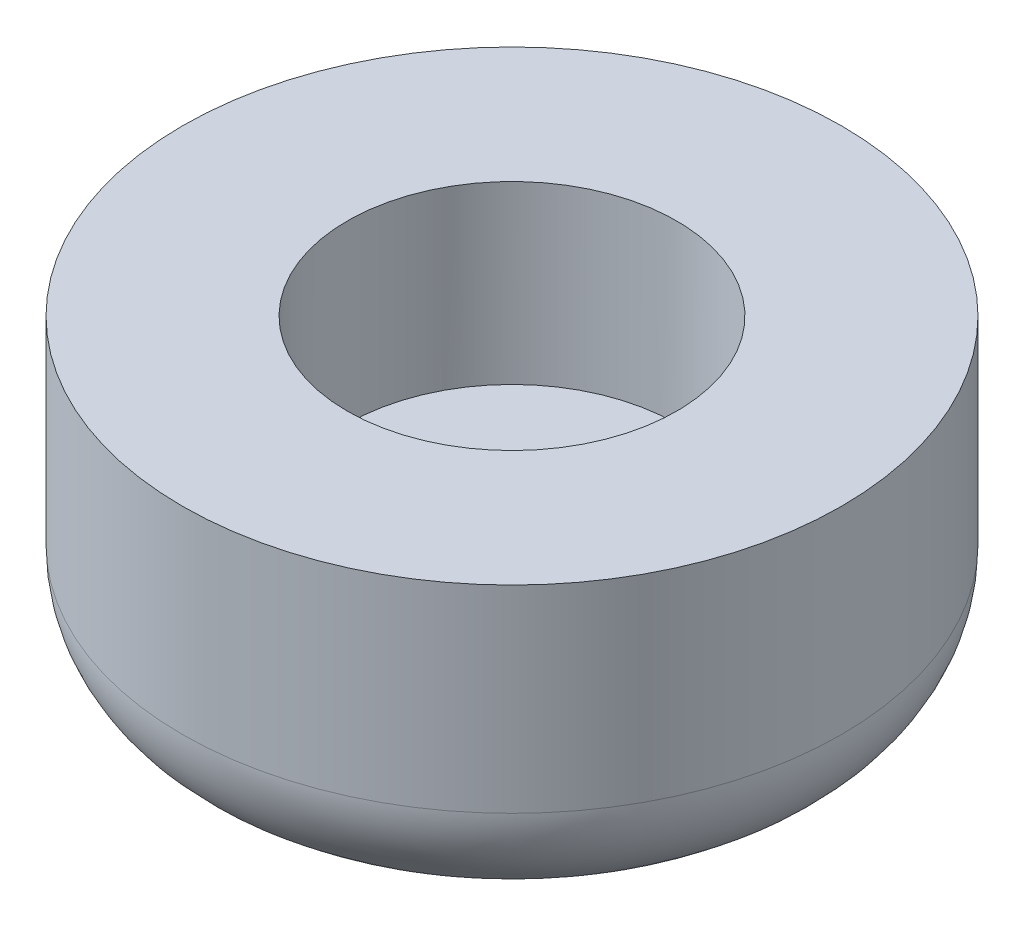
SolidWorks part; units mm, degrees
ref_plane "Спереди" through (0, 0, 0) normal (0, 0, 1) x (1, 0, 0)
ref_plane "Сверху" through (0, 0, 0) normal (0, 1, 0) x (1, 0, 0)
ref_plane "Справа" through (0, 0, 0) normal (1, 0, 0) x (0, 0, -1)
other "Configuration Table"
sketch "Эскиз1" plane through (0, 0, 0) normal (0, 1, 0) x (1, 0, 0)
  circle A0 centre (0, 0) radius 3.75
  circle A1 centre (0, 0) radius 7.5
  dimension "D1" = 7.5
  dimension "D2" = 15
extrude "Бобышка-Вытянуть1" add sketch "Эскиз1" against normal blind 7
sketch "Эскиз2" plane through (0, -7, 0) normal (0, -1, 0) x (-1, 0, 0)
  circle A0 centre (0, 0) radius 6
extrude "Бобышка-Вытянуть2" add sketch "Эскиз2" against normal blind 3
fillet "Скругление1" radius 2.5 1 edges at (0, -7, 7.5)
